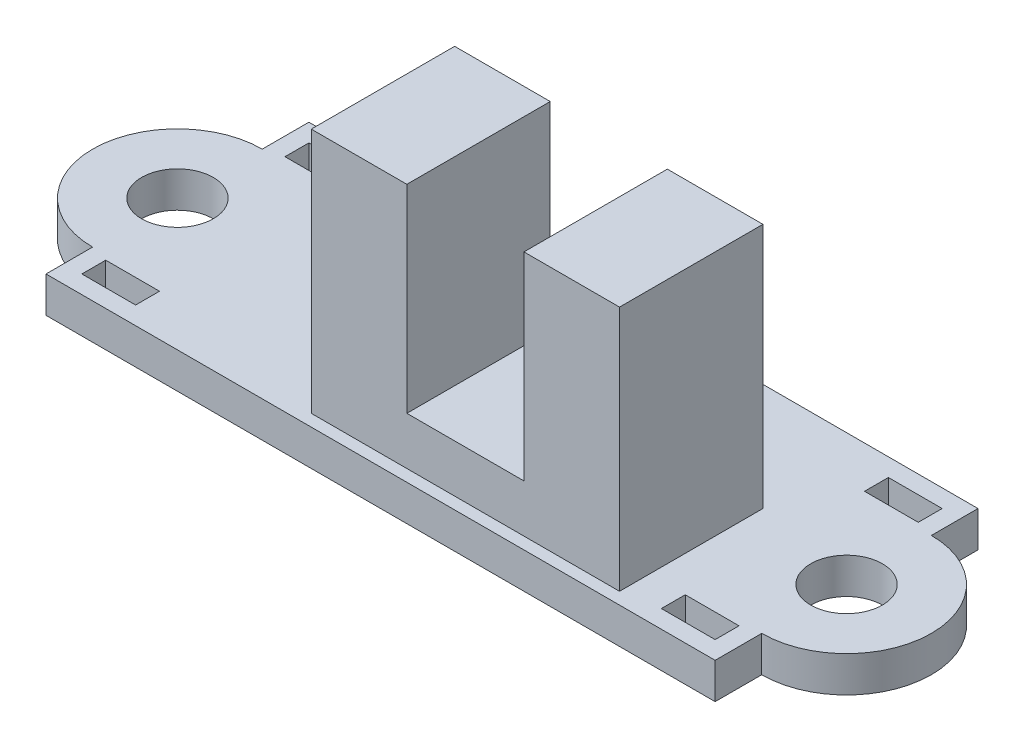
SolidWorks part; units mm, degrees
ref_plane "Front Plane" through (0, 0, 0) normal (0, 0, 1) x (1, 0, 0)
ref_plane "Top Plane" through (0, 0, 0) normal (0, 1, 0) x (1, 0, 0)
ref_plane "Right Plane" through (0, 0, 0) normal (1, 0, 0) x (0, 0, -1)
sketch "Sketch1" plane through (0, 0, 0) normal (0, 1, 0) x (1, 0, 0)
  line L9 (-14, 3.55) -> (-14, 5.5)
  line L10 (-14, 5.5) -> (14, 5.5)
  line L11 (14, 3.55) -> (14, 5.5)
  line L13 (-14, -3.55) -> (-14, -5.5)
  line L14 (-14, -5.5) -> (14, -5.5)
  line L15 (14, -3.55) -> (14, -5.5)
  circle A2 centre (-14, 0) radius 1.5
  circle A3 centre (14, 0) radius 1.5
  arc A4 (14, 3.55) -> (14, -3.55) centre (14, 0) cw
  arc A5 (-14, 3.55) -> (-14, -3.55) centre (-14, 0) ccw
  point P13 (0, 5.5)
  dimension "D4" = 3
  dimension "D8" = 3.55
  dimension "D1" = 28
  dimension "D2" = 11
extrude "PCB" add sketch "Sketch1" along normal blind 1.5
sketch "Sketch2" plane through (0, 1.5, 0) normal (0, 1, 0) x (1, 0, 0)
  line L0 (-0.825, 0) -> (0.825, 0) construction
  line L1 (-13.25, -4.75) -> (-11, -4.75)
  line L2 (-13.25, -4.75) -> (-13.25, -3.75)
  line L3 (-13.25, -3.75) -> (-11, -3.75)
  line L4 (-11, -4.75) -> (-11, -3.75)
  line L5 (-13.25, 3.75) -> (-11, 3.75)
  line L6 (-11, 4.75) -> (-11, 3.75)
  line L7 (-13.25, 4.75) -> (-11, 4.75)
  line L8 (-13.25, 4.75) -> (-13.25, 3.75)
  line L9 (0, -0.825) -> (0, 0.825) construction
  line L10 (13.25, 4.75) -> (13.25, 3.75)
  line L11 (13.25, 4.75) -> (11, 4.75)
  line L12 (11, 4.75) -> (11, 3.75)
  line L13 (13.25, 3.75) -> (11, 3.75)
  line L14 (13.25, -3.75) -> (11, -3.75)
  line L15 (11, -4.75) -> (11, -3.75)
  line L16 (13.25, -4.75) -> (11, -4.75)
  line L17 (13.25, -4.75) -> (13.25, -3.75)
  dimension "D1" = 0.75
  dimension "D2" = 0.75
  dimension "D3" = 2.25
  dimension "D4" = 1
extrude "Tab Slots" cut sketch "Sketch2" against normal through all
sketch "Sketch3" plane through (0, 1.5, 0) normal (0, 1, 0) x (1, 0, 0)
  line L1 (9.5, -5) -> (-3.4, -5)
  line L2 (9.5, -5) -> (9.5, 1)
  line L3 (9.5, 1) -> (-3.4, 1)
  line L4 (-3.4, -5) -> (-3.4, 1)
  dimension "D1" = 6
  dimension "D2" = 12.9
  dimension "D3" = 4.5
  dimension "D4" = 0.5
extrude "Sensor Body" add sketch "Sketch3" along normal blind 10.3 separate body
sketch "Sketch4" plane through (0, 11.8, 0) normal (0, 1, 0) x (1, 0, 0)
  line L0 (-3.4, -5) -> (9.5, -5) construction
  line L1 (0.6, -5) -> (5.5, -5)
  line L2 (0.6, -5) -> (0.6, 1)
  line L3 (0.6, 1) -> (5.5, 1)
  line L4 (5.5, -5) -> (5.5, 1)
  line L5 (9.5, 1) -> (-3.4, 1) construction
  dimension "D1" = 4
  dimension "D2" = 4
extrude "Sensor Slot" cut sketch "Sketch4" against normal blind 8.3
